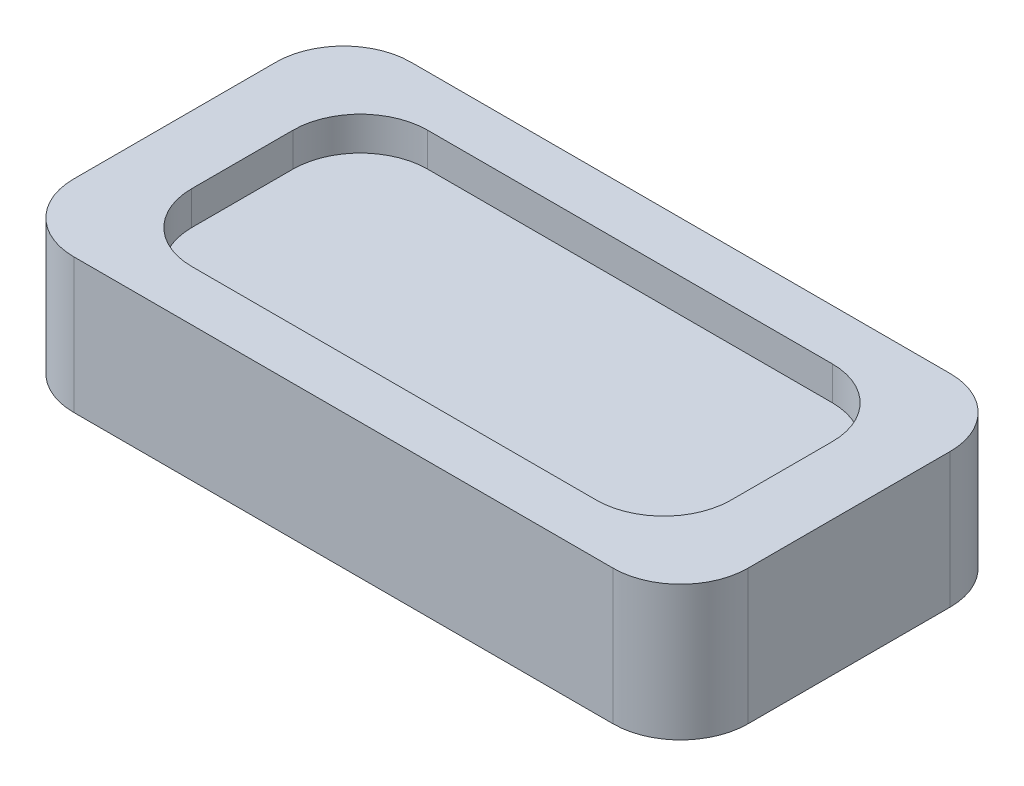
SolidWorks part; units mm, degrees
ref_plane "Front Plane" through (0, 0, 0) normal (0, 0, 1) x (1, 0, 0)
ref_plane "Top Plane" through (0, 0, 0) normal (0, 1, 0) x (1, 0, 0)
ref_plane "Right Plane" through (0, 0, 0) normal (1, 0, 0) x (0, 0, -1)
sketch "Sketch1" plane through (0, 0, 0) normal (0, 1, 0) x (1, 0, 0)
  line L1 (-50, 25) -> (50, 25)
  line L2 (-50, 25) -> (-50, -25)
  line L3 (-50, -25) -> (50, -25)
  line L4 (50, 25) -> (50, -25)
  dimension "D1" = 50
  dimension "D2" = 100
  dimension "D3" = 25
  dimension "D4" = 50
extrude "Boss-Extrude1" add sketch "Sketch1" along normal blind 20 contours L3 L4 L1 L2
sketch "Sketch2" plane through (0, 20, 0) normal (0, 1, 0) x (1, 0, 0)
  line L0 (-50, -25) -> (50, -25) construction
  line L1 (-40, 17.5) -> (40, 17.5)
  line L2 (-40, 17.5) -> (-40, -17.5)
  line L3 (-40, -17.5) -> (40, -17.5)
  line L4 (40, 17.5) -> (40, -17.5)
  line L5 (-50, 25) -> (-50, -25) construction
  dimension "D1" = 35
  dimension "D2" = 80
  dimension "D3" = 7.5
  dimension "D4" = 10
extrude "Cut-Extrude1" cut sketch "Sketch2" against normal blind 5
fillet "Fillet1" radius 10 4 edges at (-50, 10, -25) (-50, 10, 25) (50, 10, -25) (50, 10, 25)
fillet "Fillet2" radius 10 4 edges at (-40, 17.5, 17.5) (40, 17.5, 17.5) (-40, 17.5, -17.5) (40, 17.5, -17.5)
